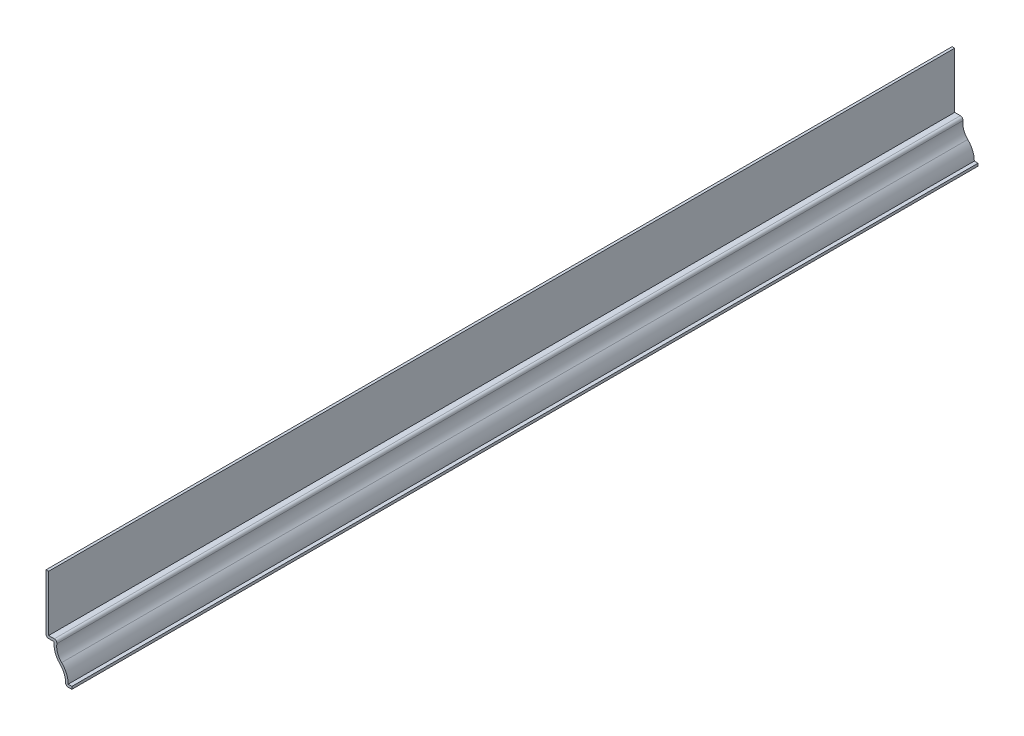
SolidWorks part; units mm, degrees
ref_plane "Front Plane" through (0, 0, 0) normal (0, 0, 1) x (1, 0, 0)
ref_plane "Top Plane" through (0, 0, 0) normal (0, 1, 0) x (1, 0, 0)
ref_plane "Right Plane" through (0, 0, 0) normal (1, 0, 0) x (0, 0, -1)
sketch "Sketch1" plane through (0, 0, 0) normal (0, 0, 1) x (1, 0, 0)
  line L0 (0, 0) -> (-3.175, 0)
  line L1 (-8.644, 15.875) -> (-12.7, 15.875)
  line L2 (-12.7, 15.875) -> (-12.7, 44.45)
  arc A0 (-3.175, 0) -> (-5.9095, 7.9375) centre (-12.376, 1.27) ccw
  arc A1 (-5.9095, 7.9375) -> (-8.644, 15.875) centre (0.5569, 14.605) cw
  point P7 (0, 0)
  point P10 (0, 0)
  point P11 (-5.7641, 7.9608)
  dimension "D1" = 44.45
  dimension "D2" = 12.7
  dimension "D3" = 28.575
  dimension "D4" = 3.175
  dimension "D5" = 3.9688
  dimension "D6" = 1.27
  dimension "D7" = 1.27
extrude "Extrude-Thin1" add sketch "Sketch1" against normal blind 444.5 thin
fillet "Fillet1" radius 1.27 3 edges at (-3.175, 0, -222.25) (-12.7, 15.875, -222.25) (-7.0483, 17.145, -222.25)
